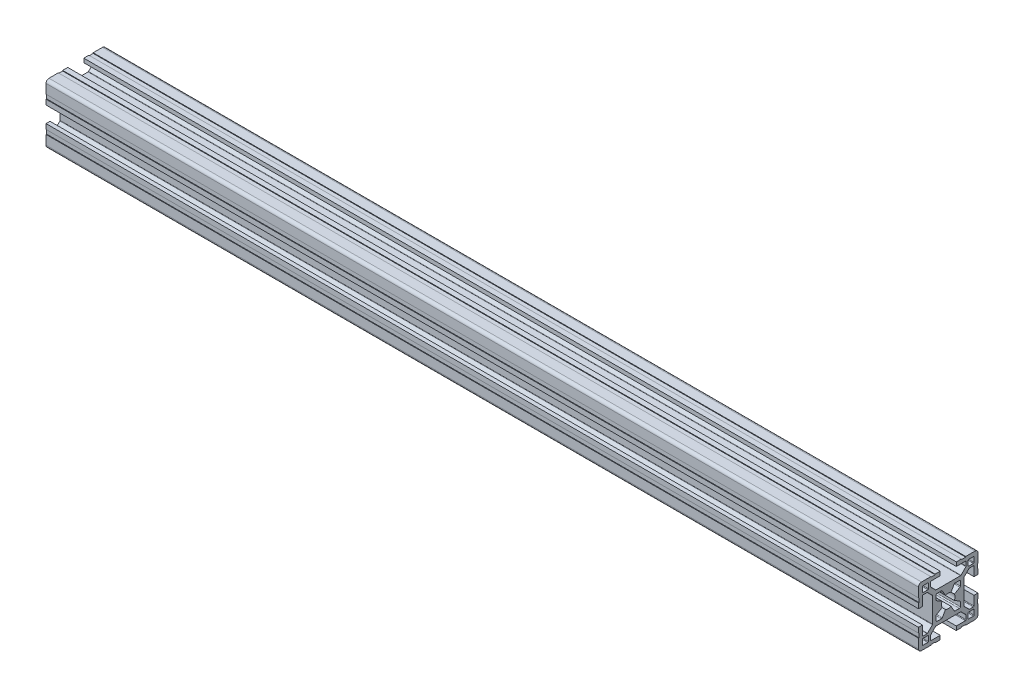
SolidWorks part; units mm, degrees
material "6063-T5"
ref_plane "Plano frontal" through (0, 0, 0) normal (0, 0, 1) x (1, 0, 0)
ref_plane "Plano superior" through (0, 0, 0) normal (0, 1, 0) x (1, 0, 0)
ref_plane "Plano direito" through (0, 0, 0) normal (1, 0, 0) x (0, 0, -1)
sketch "Esboço1" plane through (0, 0, 0) normal (0, 0, 1) x (1, 0, 0)
  line L0 (0, 0) -> (440, 0)
  point P3 (220, 0)
  dimension "D1" = 440
other "Quadrado PF30-11 - PERFIL 3030 CENTRO M8(1)"
ref_plane "Plano1" through (0, 0, 0) normal (1, 0, 0) x (0, 1, 0)
sketch "Sketch1" plane through (0, 0, 0) normal (1, 0, 0) x (0, 1, 0)
  line L0 (-6.1, -3.4254) -> (-6.1, -5.6)
  line L1 (-5.6, -6.1) -> (-3.4254, -6.1)
  line L2 (3.4254, -6.1) -> (5.6, -6.1)
  line L3 (6.1, -5.6) -> (6.1, -3.4254)
  line L4 (6.1, 3.4254) -> (6.1, 5.6)
  line L5 (5.6, 6.1) -> (3.4254, 6.1)
  line L6 (-3.4254, 6.1) -> (-5.6, 6.1)
  line L7 (-6.1, 5.6) -> (-6.1, 3.4254)
  line L8 (15, 6.6) -> (14.7, 6.6)
  line L9 (5.85, -2.9924) -> (3.097, -1.403)
  line L10 (10, 12.7) -> (10, 10.3)
  line L11 (13, -12.7) -> (13, -10.3)
  line L12 (-10.3, -10) -> (-12.7, -10)
  line L13 (-13, 12.7) -> (-13, 10.3)
  line L14 (3.097, 1.403) -> (5.85, 2.9924)
  line L15 (2.9924, 5.85) -> (1.403, 3.097)
  line L16 (-1.403, 3.097) -> (-2.9924, 5.85)
  line L17 (-5.85, 2.9924) -> (-3.097, 1.403)
  line L18 (-3.097, -1.403) -> (-5.85, -2.9924)
  line L19 (-2.9924, -5.85) -> (-1.403, -3.097)
  line L20 (1.403, -3.097) -> (2.9924, -5.85)
  line L21 (10.3, 10) -> (12.7, 10)
  line L22 (13, 10.3) -> (13, 12.7)
  line L23 (12.7, 13) -> (10.3, 13)
  line L24 (12.7, -10) -> (10.3, -10)
  line L25 (10, -10.3) -> (10, -12.7)
  line L26 (10.3, -13) -> (12.7, -13)
  line L27 (-13, -10.3) -> (-13, -12.7)
  line L28 (-12.7, -13) -> (-10.3, -13)
  line L29 (-10, -12.7) -> (-10, -10.3)
  line L30 (-12.7, 10) -> (-10.3, 10)
  line L31 (-10, 10.3) -> (-10, 12.7)
  line L32 (-10.3, 13) -> (-12.7, 13)
  line L33 (15, 4.05) -> (15, 6.6)
  line L34 (13, 4.05) -> (15, 4.05)
  line L35 (13, 8.7) -> (13, 4.05)
  line L36 (10.6799, 9) -> (12.7, 9)
  line L37 (7.9879, 6.4322) -> (10.4678, 8.9121)
  line L38 (7.9, -6.2201) -> (7.9, 6.2201)
  line L39 (10.4678, -8.9121) -> (7.9879, -6.4322)
  line L40 (12.7, -9) -> (10.6799, -9)
  line L41 (13, -4.05) -> (13, -8.7)
  line L42 (15, -4.05) -> (13, -4.05)
  line L43 (15, -6.6) -> (15, -4.05)
  line L44 (14.7, -6.6) -> (15, -6.6)
  line L45 (14.7, -8.8) -> (14.7, -6.6)
  line L46 (15, -8.8) -> (14.7, -8.8)
  line L47 (15, -13.5) -> (15, -8.8)
  line L48 (8.8, -15) -> (13.5, -15)
  line L49 (8.8, -14.7) -> (8.8, -15)
  line L50 (6.6, -14.7) -> (8.8, -14.7)
  line L51 (6.6, -15) -> (6.6, -14.7)
  line L52 (4.05, -15) -> (6.6, -15)
  line L53 (4.05, -13) -> (4.05, -15)
  line L54 (8.7, -13) -> (4.05, -13)
  line L55 (9, -10.6799) -> (9, -12.7)
  line L56 (6.4322, -7.9879) -> (8.9121, -10.4678)
  line L57 (-6.2201, -7.9) -> (6.2201, -7.9)
  line L58 (-8.9121, -10.4678) -> (-6.4322, -7.9879)
  line L59 (-9, -12.7) -> (-9, -10.6799)
  line L60 (-4.05, -13) -> (-8.7, -13)
  line L61 (-4.05, -15) -> (-4.05, -13)
  line L62 (-6.6, -15) -> (-4.05, -15)
  line L63 (-6.6, -14.7) -> (-6.6, -15)
  line L64 (-8.8, -14.7) -> (-6.6, -14.7)
  line L65 (-8.8, -15) -> (-8.8, -14.7)
  line L66 (-13.5, -15) -> (-8.8, -15)
  line L67 (-15, -8.8) -> (-15, -13.5)
  line L68 (-14.7, -8.8) -> (-15, -8.8)
  line L69 (-14.7, -6.6) -> (-14.7, -8.8)
  line L70 (-15, -6.6) -> (-14.7, -6.6)
  line L71 (-15, -4.05) -> (-15, -6.6)
  line L72 (-13, -4.05) -> (-15, -4.05)
  line L73 (-13, -8.7) -> (-13, -4.05)
  line L74 (-10.6799, -9) -> (-12.7, -9)
  line L75 (-7.9879, -6.4322) -> (-10.4678, -8.9121)
  line L76 (-7.9, 6.2201) -> (-7.9, -6.2201)
  line L77 (-10.4678, 8.9121) -> (-7.9879, 6.4322)
  line L78 (-12.7, 9) -> (-10.6799, 9)
  line L79 (-13, 4.05) -> (-13, 8.7)
  line L80 (-15, 4.05) -> (-13, 4.05)
  line L81 (-15, 6.6) -> (-15, 4.05)
  line L82 (-14.7, 6.6) -> (-15, 6.6)
  line L83 (-14.7, 8.8) -> (-14.7, 6.6)
  line L84 (-15, 8.8) -> (-14.7, 8.8)
  line L85 (-15, 13.5) -> (-15, 8.8)
  line L86 (-8.8, 15) -> (-13.5, 15)
  line L87 (-8.8, 14.7) -> (-8.8, 15)
  line L88 (-6.6, 14.7) -> (-8.8, 14.7)
  line L89 (-6.6, 15) -> (-6.6, 14.7)
  line L90 (-4.05, 15) -> (-6.6, 15)
  line L91 (-4.05, 13) -> (-4.05, 15)
  line L92 (-8.7, 13) -> (-4.05, 13)
  line L93 (-9, 10.6799) -> (-9, 12.7)
  line L94 (-6.4322, 7.9879) -> (-8.9121, 10.4678)
  line L95 (6.2201, 7.9) -> (-6.2201, 7.9)
  line L96 (8.9121, 10.4678) -> (6.4322, 7.9879)
  line L97 (9, 12.7) -> (9, 10.6799)
  line L98 (4.05, 13) -> (8.7, 13)
  line L99 (4.05, 15) -> (4.05, 13)
  line L100 (6.6, 15) -> (4.05, 15)
  line L101 (6.6, 14.7) -> (6.6, 15)
  line L102 (8.8, 14.7) -> (6.6, 14.7)
  line L103 (8.8, 15) -> (8.8, 14.7)
  line L104 (13.5, 15) -> (8.8, 15)
  line L105 (15, 8.8) -> (15, 13.5)
  line L106 (14.7, 8.8) -> (15, 8.8)
  line L107 (14.7, 6.6) -> (14.7, 8.8)
  arc A0 (-5.85, -2.9924) -> (-6.1, -3.4254) centre (-5.6, -3.4254) ccw
  arc A1 (-6.1, -5.6) -> (-5.6, -6.1) centre (-5.6, -5.6) ccw
  arc A2 (-3.4254, -6.1) -> (-2.9924, -5.85) centre (-3.4254, -5.6) ccw
  arc A3 (2.9924, -5.85) -> (3.4254, -6.1) centre (3.4254, -5.6) ccw
  arc A4 (5.6, -6.1) -> (6.1, -5.6) centre (5.6, -5.6) ccw
  arc A5 (6.1, -3.4254) -> (5.85, -2.9924) centre (5.6, -3.4254) ccw
  arc A6 (5.85, 2.9924) -> (6.1, 3.4254) centre (5.6, 3.4254) ccw
  arc A7 (6.1, 5.6) -> (5.6, 6.1) centre (5.6, 5.6) ccw
  arc A8 (3.4254, 6.1) -> (2.9924, 5.85) centre (3.4254, 5.6) ccw
  arc A9 (-2.9924, 5.85) -> (-3.4254, 6.1) centre (-3.4254, 5.6) ccw
  arc A10 (-5.6, 6.1) -> (-6.1, 5.6) centre (-5.6, 5.6) ccw
  arc A11 (-6.1, 3.4254) -> (-5.85, 2.9924) centre (-5.6, 3.4254) ccw
  arc A12 (3.097, -1.403) -> (3.097, 1.403) centre (0, 0) ccw
  arc A13 (1.403, 3.097) -> (-1.403, 3.097) centre (0, 0) ccw
  arc A14 (-3.097, 1.403) -> (-3.097, -1.403) centre (0, 0) ccw
  arc A15 (-1.403, -3.097) -> (1.403, -3.097) centre (0, 0) ccw
  arc A16 (10, 10.3) -> (10.3, 10) centre (10.3, 10.3) ccw
  arc A17 (12.7, 10) -> (13, 10.3) centre (12.7, 10.3) ccw
  arc A18 (13, 12.7) -> (12.7, 13) centre (12.7, 12.7) ccw
  arc A19 (10.3, 13) -> (10, 12.7) centre (10.3, 12.7) ccw
  arc A20 (13, -10.3) -> (12.7, -10) centre (12.7, -10.3) ccw
  arc A21 (10.3, -10) -> (10, -10.3) centre (10.3, -10.3) ccw
  arc A22 (10, -12.7) -> (10.3, -13) centre (10.3, -12.7) ccw
  arc A23 (12.7, -13) -> (13, -12.7) centre (12.7, -12.7) ccw
  arc A24 (-12.7, -10) -> (-13, -10.3) centre (-12.7, -10.3) ccw
  arc A25 (-13, -12.7) -> (-12.7, -13) centre (-12.7, -12.7) ccw
  arc A26 (-10.3, -13) -> (-10, -12.7) centre (-10.3, -12.7) ccw
  arc A27 (-10, -10.3) -> (-10.3, -10) centre (-10.3, -10.3) ccw
  arc A28 (-13, 10.3) -> (-12.7, 10) centre (-12.7, 10.3) ccw
  arc A29 (-10.3, 10) -> (-10, 10.3) centre (-10.3, 10.3) ccw
  arc A30 (-10, 12.7) -> (-10.3, 13) centre (-10.3, 12.7) ccw
  arc A31 (-12.7, 13) -> (-13, 12.7) centre (-12.7, 12.7) ccw
  arc A32 (13, 8.7) -> (12.7, 9) centre (12.7, 8.7) ccw
  arc A33 (10.6799, 9) -> (10.4678, 8.9121) centre (10.6799, 8.7) ccw
  arc A34 (7.9879, 6.4322) -> (7.9, 6.2201) centre (8.2, 6.2201) ccw
  arc A35 (7.9, -6.2201) -> (7.9879, -6.4322) centre (8.2, -6.2201) ccw
  arc A36 (10.4678, -8.9121) -> (10.6799, -9) centre (10.6799, -8.7) ccw
  arc A37 (12.7, -9) -> (13, -8.7) centre (12.7, -8.7) ccw
  arc A38 (13.5, -15) -> (15, -13.5) centre (13.5, -13.5) ccw
  arc A39 (8.7, -13) -> (9, -12.7) centre (8.7, -12.7) ccw
  arc A40 (9, -10.6799) -> (8.9121, -10.4678) centre (8.7, -10.6799) ccw
  arc A41 (6.4322, -7.9879) -> (6.2201, -7.9) centre (6.2201, -8.2) ccw
  arc A42 (-6.2201, -7.9) -> (-6.4322, -7.9879) centre (-6.2201, -8.2) ccw
  arc A43 (-8.9121, -10.4678) -> (-9, -10.6799) centre (-8.7, -10.6799) ccw
  arc A44 (-9, -12.7) -> (-8.7, -13) centre (-8.7, -12.7) ccw
  arc A45 (-15, -13.5) -> (-13.5, -15) centre (-13.5, -13.5) ccw
  arc A46 (-13, -8.7) -> (-12.7, -9) centre (-12.7, -8.7) ccw
  arc A47 (-10.6799, -9) -> (-10.4678, -8.9121) centre (-10.6799, -8.7) ccw
  arc A48 (-7.9879, -6.4322) -> (-7.9, -6.2201) centre (-8.2, -6.2201) ccw
  arc A49 (-7.9, 6.2201) -> (-7.9879, 6.4322) centre (-8.2, 6.2201) ccw
  arc A50 (-10.4678, 8.9121) -> (-10.6799, 9) centre (-10.6799, 8.7) ccw
  arc A51 (-12.7, 9) -> (-13, 8.7) centre (-12.7, 8.7) ccw
  arc A52 (-13.5, 15) -> (-15, 13.5) centre (-13.5, 13.5) ccw
  arc A53 (-8.7, 13) -> (-9, 12.7) centre (-8.7, 12.7) ccw
  arc A54 (-9, 10.6799) -> (-8.9121, 10.4678) centre (-8.7, 10.6799) ccw
  arc A55 (-6.4322, 7.9879) -> (-6.2201, 7.9) centre (-6.2201, 8.2) ccw
  arc A56 (6.2201, 7.9) -> (6.4322, 7.9879) centre (6.2201, 8.2) ccw
  arc A57 (8.9121, 10.4678) -> (9, 10.6799) centre (8.7, 10.6799) ccw
  arc A58 (9, 12.7) -> (8.7, 13) centre (8.7, 12.7) ccw
  arc A59 (15, 13.5) -> (13.5, 15) centre (13.5, 13.5) ccw
  point P1 (0, 0)
  point P2 (0, 0)
  point P3 (-15, -15)
  point P4 (0, -15)
  point P5 (-15, 0)
  point P230 (-15, 15)
  point P231 (0, 15)
  point P232 (15, 15)
  point P233 (15, 0)
  point P234 (15, -15)
  point P235 (0, -15)
  point P236 (-15, -15)
  point P237 (-15, 0)
  point P238 (0, 0)
  point P239 (0, 0)
